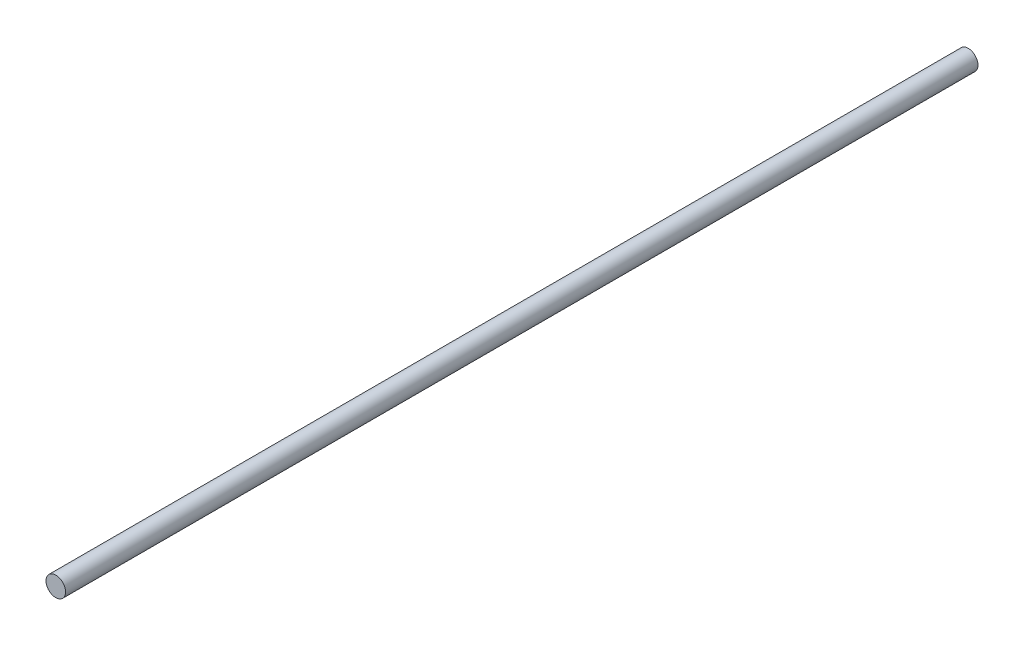
SolidWorks part; units mm, degrees
ref_plane "前视基准面" through (0, 0, 0) normal (0, 0, 1) x (1, 0, 0)
ref_plane "上视基准面" through (0, 0, 0) normal (0, 1, 0) x (1, 0, 0)
ref_plane "右视基准面" through (0, 0, 0) normal (1, 0, 0) x (0, 0, -1)
sketch "草图1" plane through (0, 0, 0) normal (0, 0, 1) x (1, 0, 0)
  circle A0 centre (0, 0) radius 3
  dimension "D1" = 6
extrude "凸台-拉伸1" add sketch "草图1" along normal blind 280
